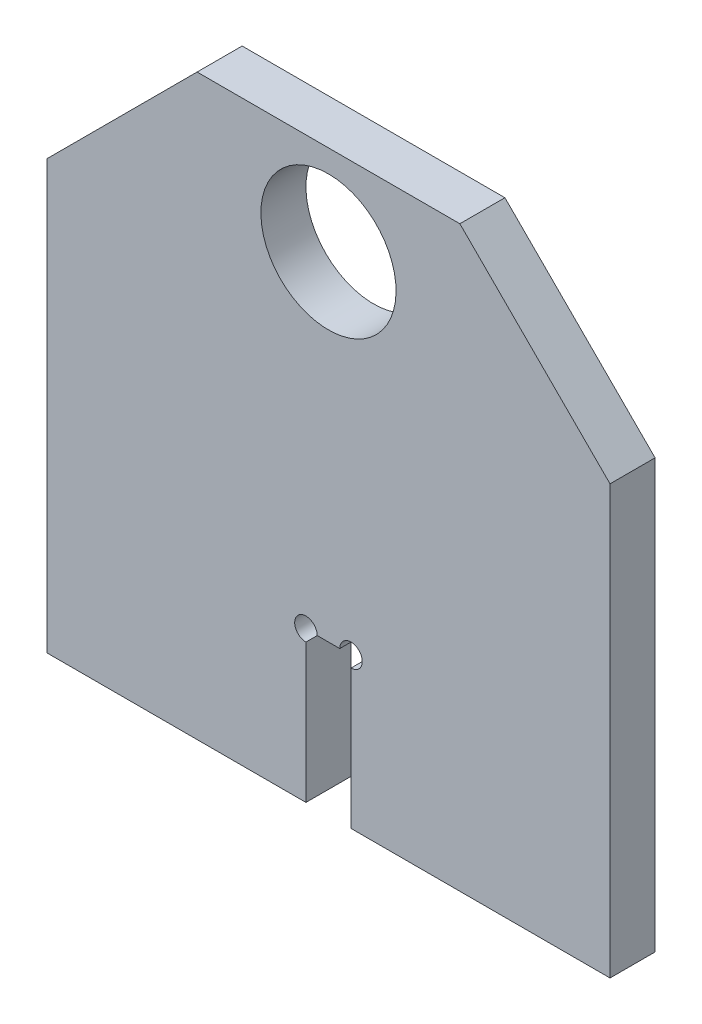
SolidWorks part; units mm, degrees
material "1.0553 (S355J0)"
ref_plane "Front Plane" through (0, 0, 0) normal (0, 0, 1) x (1, 0, 0)
ref_plane "Top Plane" through (0, 0, 0) normal (0, 1, 0) x (1, 0, 0)
ref_plane "Right Plane" through (0, 0, 0) normal (1, 0, 0) x (0, 0, -1)
sketch "Sketch1" plane through (0, 0, 0) normal (0, 0, 1) x (1, 0, 0)
  line L0 (0, 140) -> (0, 121.5) construction
  line L1 (-3, 140) -> (3, 140) construction
  line L2 (-3, 121.5) -> (3, 121.5) construction
  line L3 (-3, 140) -> (3, 140) construction
  line L4 (37.5, 100) -> (-37.5, 100) construction
  line L5 (37.5, 100) -> (37.5, 157)
  line L6 (17.5, 177) -> (-17.5, 177)
  line L7 (-37.5, 100) -> (-37.5, 157)
  line L8 (37.5, 100) -> (-37.5, 177) construction
  line L9 (37.5, 177) -> (-37.5, 100) construction
  line L12 (-17.5, 177) -> (-37.5, 157)
  line L13 (37.5, 157) -> (17.5, 177)
  line L14 (-37.5, 100) -> (-3, 100)
  line L15 (-3, 140) -> (-30, 140) construction
  line L17 (-3, 100) -> (-3, 120)
  line L18 (-3, 120) -> (3, 120)
  line L19 (3, 120) -> (3, 100)
  line L20 (3, 140) -> (3, 60) construction
  line L21 (3, 100) -> (37.5, 100)
  circle A0 centre (0.0001, 165) radius 9
  circle A1 centre (-3, 120) radius 1.5
  circle A2 centre (3, 120) radius 1.5
  point P6 (0, 138.5)
  dimension "D3" = 3
  dimension "D4" = 3
  dimension "D8" = 18
  dimension "D2" = 37
  dimension "D7" = 75
  dimension "D9" = 25
extrude "Boss-Extrude1" add sketch "Sketch1" along normal up to surface (6 mm away) contours A2 L19 L21 L5 L13 L6 L12 L7 L14 L17 A1 L18 A0
